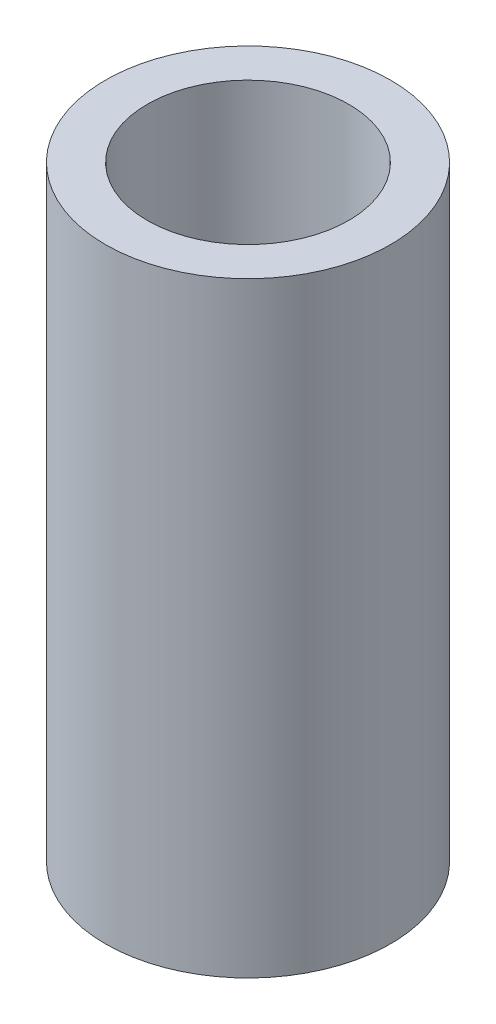
SolidWorks part; units mm, degrees
ref_plane "Front" through (0, 0, 0) normal (0, 0, 1) x (1, 0, 0)
ref_plane "Top" through (0, 0, 0) normal (0, 1, 0) x (1, 0, 0)
ref_plane "Right" through (0, 0, 0) normal (1, 0, 0) x (0, 0, -1)
sketch "Sketch1" plane through (0, 0, 0) normal (0, 1, 0) x (1, 0, 0)
  circle A0 centre (0, 0) radius 6.731
  circle A1 centre (0, 0) radius 9.525
  dimension "D1" = 19.05
  dimension "D2" = 13.462
extrude "Boss-Extrude1" add sketch "Sketch1" along normal blind 40.4708
